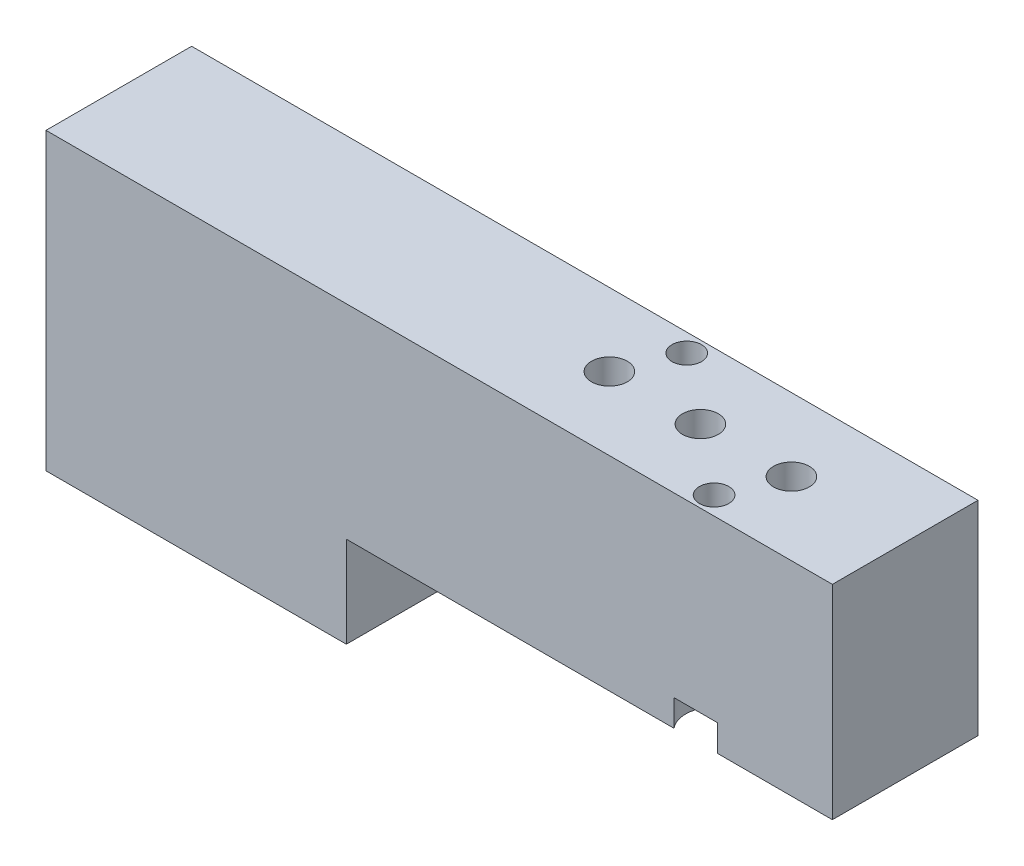
SolidWorks part; units mm, degrees
material "6061 Alloy"
ref_plane "Front" through (0, 0, 0) normal (0, 0, 1) x (1, 0, 0)
ref_plane "Top" through (0, 0, 0) normal (0, 1, 0) x (1, 0, 0)
ref_plane "Right" through (0, 0, 0) normal (1, 0, 0) x (0, 0, -1)
sketch "Sketch1" plane through (0, 0, 0) normal (0, 0, 1) x (1, 0, 0)
  line L1 (0, 0) -> (54.864, 0)
  line L2 (0, 0) -> (0, 14.224)
  line L3 (0, 14.224) -> (54.864, 14.224)
  line L4 (54.864, 0) -> (54.864, 14.224)
  dimension "D1" = 54.864
  dimension "D2" = 14.224
extrude "Base-Extrude" add sketch "Sketch1" against normal blind 10.16
sketch "Sketch2" plane through (0, 0, 0) normal (0, -1, 0) x (1, 0, 0)
  line L0 (0, -10.16) -> (54.864, -10.16) construction
  line L1 (0, 0) -> (20.955, 0)
  line L2 (0, 0) -> (0, -10.16)
  line L3 (0, -10.16) -> (20.955, -10.16)
  line L4 (20.955, 0) -> (20.955, -10.16)
  dimension "D1" = 20.955
extrude "Boss-Extrude1" add sketch "Sketch2" along normal blind 6.35
hole_wizard "M3x0.5 Tapped Hole1" positions "Sketch4" profile "Sketch3" tap size "M3x0.5" standard "Ansi Metric"
sketch "Sketch4" plane through (0, 14.224, 0) normal (0, 1, 0) x (-1, 0, 0)
  line L0 (-54.864, -10.16) -> (-54.864, 0) construction
  line L1 (-54.864, 0) -> (0, 0) construction
  point P0 (-46.9265, -5.08)
  point P1 (-40.5765, -5.08)
  point P2 (-34.2265, -5.08)
  dimension "D1" = 7.9375
  dimension "D2" = 6.35
  dimension "D3" = 6.35
  dimension "D4" = 5.08
  dimension "D5" = 5.08
  dimension "D6" = 5.08
sketch "Sketch3" plane through (46.9265, 14.224, -5.08) normal (1, 0, 0) x (0, 0, 1)
  line L0 (0, 0) -> (0, 8.2511)
  line L1 (0, 8.2511) -> (1.25, 7.5)
  line L2 (1.25, 7.5) -> (1.25, 0)
  line L5 (1.25, 0) -> (0, 0)
  line L10 (0, 8.2511) -> (-1.25, 7.5) construction
  line L11 (0, -6.35) -> (0, 107.95) construction
  dimension "Hole Dia." = 2.5
  dimension "Hole Depth" = 7.5
  dimension "Drill Angle" = 118
cosmetic thread "Cosmetic Thread1" parameters "D1"=6, "D2"=3
cosmetic thread "Cosmetic Thread2" parameters "D1"=6, "D2"=3
cosmetic thread "Cosmetic Thread3" parameters "D1"=6, "D2"=3
hole_wizard "CBORE for #1 Socket Head Cap Screw1" positions "Sketch8" profile "Sketch7" counterbore size "#1" standard "Ansi Inch"
sketch "Sketch8" plane through (0, 0, 0) normal (0, -1, 0) x (1, 0, 0)
  line L0 (20.955, 0) -> (54.864, 0) construction
  line L1 (20.955, -10.16) -> (54.864, -10.16) construction
  line L2 (54.864, -10.16) -> (54.864, 0) construction
  point P0 (45.339, -1.27)
  point P1 (35.814, -8.89)
  dimension "D1" = 1.27
  dimension "D2" = 1.27
  dimension "D3" = 9.525
  dimension "D4" = 19.05
sketch "Sketch7" plane through (45.339, 0, -1.27) normal (1, 0, 0) x (0, 0, -1)
  line L0 (0, 0) -> (0, 23.4781)
  line L1 (0, 23.4781) -> (1.0287, 22.86)
  line L2 (1.0287, 22.86) -> (1.0287, 1.8542)
  line L3 (1.0287, 1.8542) -> (1.985, 1.8542)
  line L4 (1.985, 1.8542) -> (1.985, 0)
  line L5 (1.985, 0) -> (0, 0)
  line L10 (0, 23.4781) -> (-1.0287, 22.86) construction
  line L11 (0, -6.35) -> (0, 107.95) construction
  dimension "Hole Dia." = 2.0574
  dimension "Hole Depth" = 22.86
  dimension "C'Bore Dia." = 3.97
  dimension "C'Bore Depth" = 1.8542
  dimension "Drill Angle" = 118
hole_wizard "M3x0.5 Tapped Hole2" positions "Sketch10" profile "Sketch9" tap size "M3x0.5" standard "Ansi Metric"
sketch "Sketch10" plane through (0, 0, 0) normal (0, -1, 0) x (1, 0, 0)
  line L0 (37.3396, -10.16) -> (54.864, -10.16) construction
  line L1 (20.955, 0) -> (43.8134, 0) construction
  line L2 (54.864, -10.16) -> (54.864, 0) construction
  point P0 (43.7642, -6.985)
  point P1 (37.4142, -3.175)
  dimension "D1" = 3.175
  dimension "D2" = 3.175
  dimension "D3" = 11.0998
  dimension "D4" = 17.4498
cosmetic thread "Cosmetic Thread4" parameters "D1"=6, "D2"=3
cosmetic thread "Cosmetic Thread5" parameters "D1"=6, "D2"=3
sketch "Sketch9" plane through (43.7642, 0, -6.985) normal (1, 0, 0) x (0, 0, -1)
  line L0 (0, 0) -> (0, 8.2511)
  line L1 (0, 8.2511) -> (1.25, 7.5)
  line L2 (1.25, 7.5) -> (1.25, 0)
  line L5 (1.25, 0) -> (0, 0)
  line L10 (0, 8.2511) -> (-1.25, 7.5) construction
  line L11 (0, -6.35) -> (0, 107.95) construction
  dimension "Hole Dia." = 2.5
  dimension "Hole Depth" = 7.5
  dimension "Drill Angle" = 118
sketch "Sketch11" plane through (0, 14.224, 0) normal (0, 1, 0) x (-1, 0, 0)
  line L0 (-54.864, 0) -> (0, 0) construction
  line L1 (-46.9265, 0.3407) -> (-43.7515, 0.3407)
  line L2 (-46.9265, 0.3407) -> (-46.9265, -2.286)
  line L3 (-46.9265, -2.286) -> (-43.7515, -2.286)
  line L4 (-43.7515, 0.3407) -> (-43.7515, -2.286)
  line L5 (-37.4015, -7.874) -> (-34.2265, -7.874)
  line L6 (-37.4015, -7.874) -> (-37.4015, -10.3694)
  line L7 (-37.4015, -10.3694) -> (-34.2265, -10.3694)
  line L8 (-34.2265, -7.874) -> (-34.2265, -10.3694)
  line L9 (-54.864, -10.16) -> (0, -10.16) construction
  line L10 (-54.864, -10.16) -> (-54.864, 0) construction
  dimension "D1" = 3.175
  dimension "D2" = 3.175
  dimension "D3" = 2.286
  dimension "D4" = 2.286
  dimension "D5" = 7.9375
  dimension "D6" = 6.35
extrude "Cut-Extrude1" cut sketch "Sketch11" against normal up to surface (14.224 mm away)
